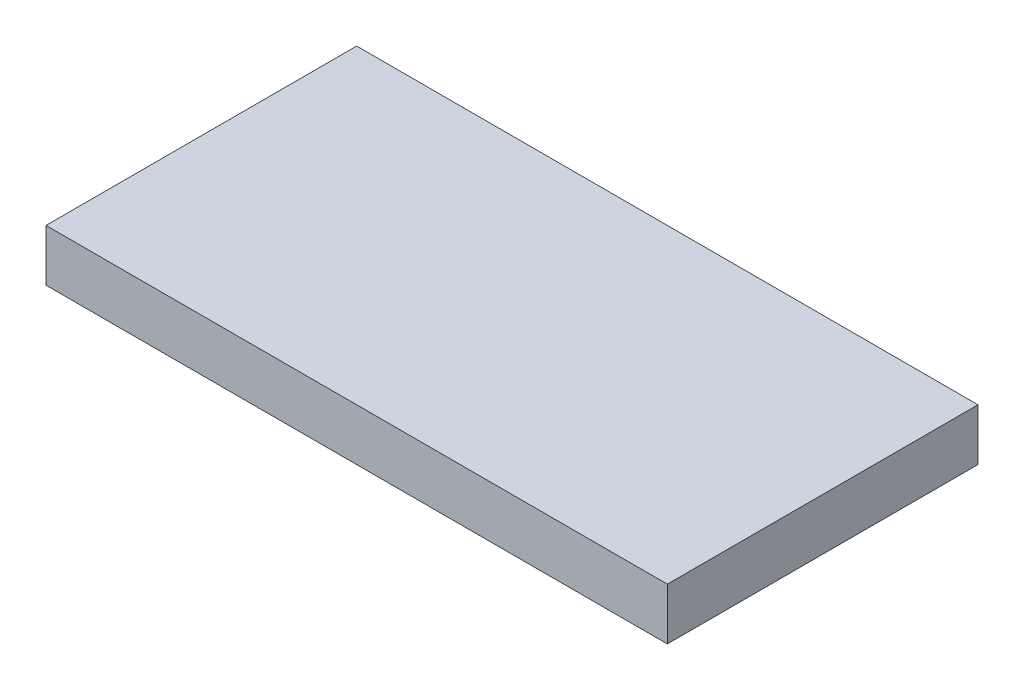
SolidWorks part; units mm, degrees
material "Polyurethane Foam Rigid"
ref_plane "Front Plane" through (0, 0, 0) normal (0, 0, 1) x (1, 0, 0)
ref_plane "Top Plane" through (0, 0, 0) normal (0, 1, 0) x (1, 0, 0)
ref_plane "Right Plane" through (0, 0, 0) normal (1, 0, 0) x (0, 0, -1)
sketch "Sketch1" plane through (0, 0, 0) normal (0, 1, 0) x (1, 0, 0)
  line L1 (-152.4, 76.2) -> (152.4, 76.2)
  line L2 (-152.4, 76.2) -> (-152.4, -76.2)
  line L3 (-152.4, -76.2) -> (152.4, -76.2)
  line L4 (152.4, 76.2) -> (152.4, -76.2)
  point P4 (0, 76.2)
  point P6 (-152.4, 0)
  dimension "D1" = 304.8
  dimension "D2" = 152.4
extrude "Boss-Extrude1" add sketch "Sketch1" along normal mid plane 25.4
